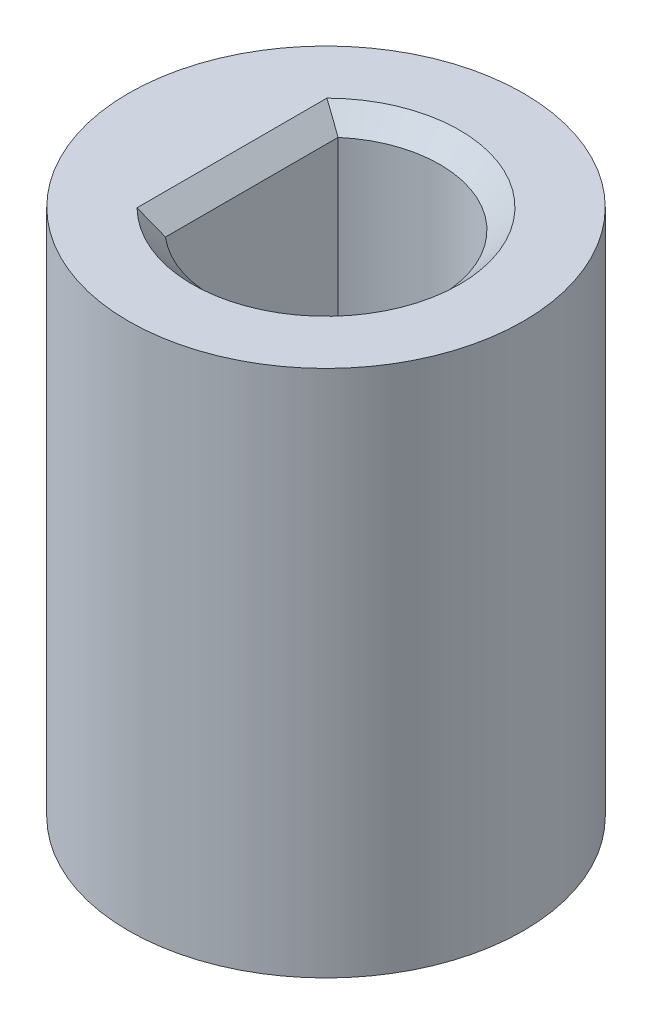
SolidWorks part; units mm, degrees
ref_plane "Front Plane" through (0, 0, 0) normal (0, 0, 1) x (1, 0, 0)
ref_plane "Top Plane" through (0, 0, 0) normal (0, 1, 0) x (1, 0, 0)
ref_plane "Right Plane" through (0, 0, 0) normal (1, 0, 0) x (0, 0, -1)
sketch "Sketch1" plane through (0, 0, 0) normal (0, 1, 0) x (1, 0, 0)
  line L0 (1.725, 1.2172) -> (1.725, -5.1573) construction
  line L2 (-1.125, 1.3077) -> (-1.125, -1.3077)
  circle A0 centre (0, 0) radius 2.9925
  arc A1 (-1.125, -1.3077) -> (-1.125, 1.3077) centre (0, 0) ccw
  point P10 (-1.231, 1.4068)
  point P12 (-1.2714, -1.3704)
  dimension "D1" = 1.725
  dimension "D3" = 2.85
extrude "Boss-Extrude1" add sketch "Sketch1" along normal blind 8
chamfer "Chamfer2" distance 0.3 angle 45 2 edges at (1.725, 8, 0) (-1.125, 8, 0)
